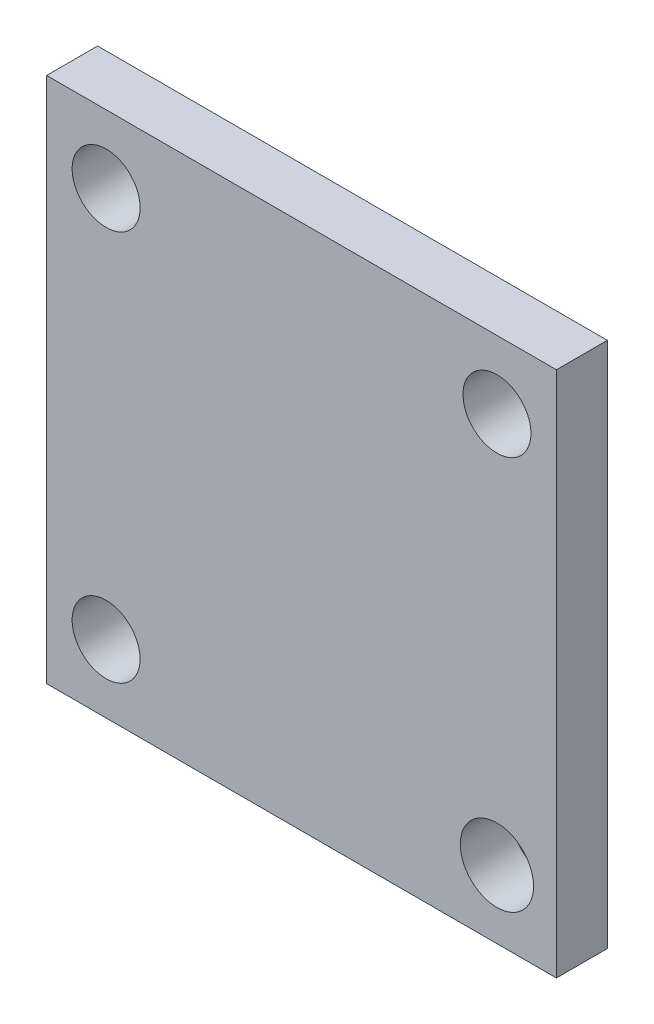
SolidWorks part; units mm, degrees
ref_plane "Front Plane" through (0, 0, 0) normal (0, 0, 1) x (1, 0, 0)
ref_plane "Top Plane" through (0, 0, 0) normal (0, 1, 0) x (1, 0, 0)
ref_plane "Right Plane" through (0, 0, 0) normal (1, 0, 0) x (0, 0, -1)
sketch "Sketch2" plane through (0, 0, 0) normal (0, 0, 1) x (1, 0, 0)
  line L0 (15.0011, -15.5011) -> (-15.0011, -15.5011)
  line L1 (15.0011, -15.5011) -> (15.0011, 15.5011)
  line L2 (15.0011, 15.5011) -> (-15.0011, 15.5011)
  line L3 (-15.0011, -15.5011) -> (-15.0011, 15.5011)
  circle A0 centre (-11.4989, 11.5033) radius 2
  circle A1 centre (11.5033, 11.5011) radius 2
  circle A2 centre (-11.5011, -11.4989) radius 2
  circle A3 centre (11.5011, -11.5011) radius 2.1563
  dimension "D1" = 4
  dimension "D2" = 4
  dimension "D3" = 4
  dimension "D4" = 4.3125
extrude "Boss-Extrude1" add sketch "Sketch2" along normal blind 3
